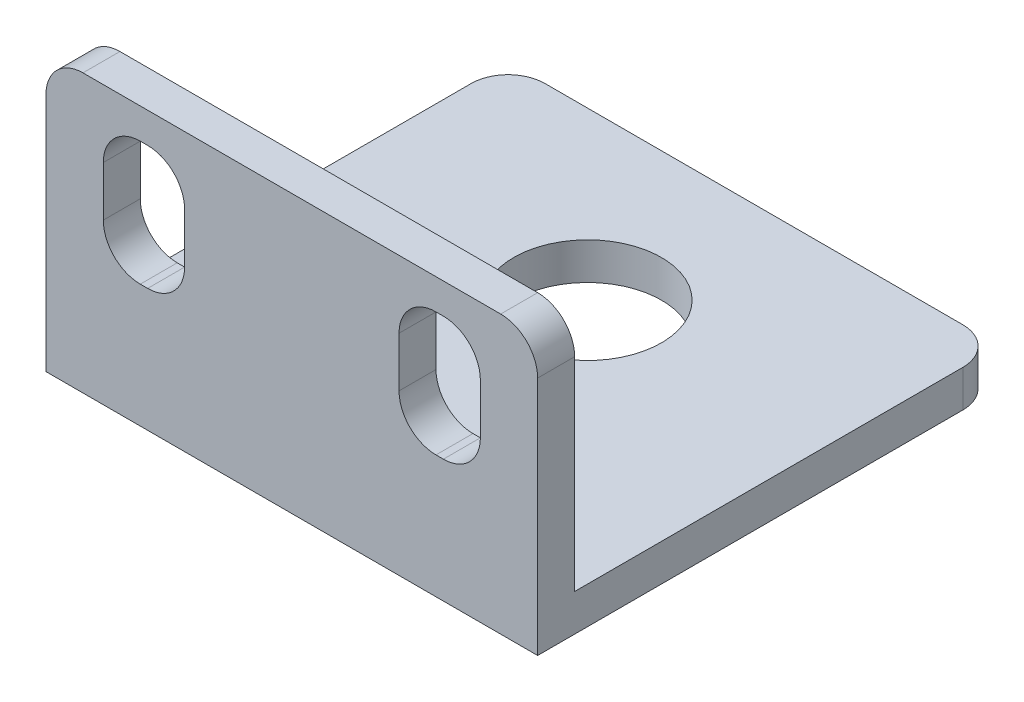
SolidWorks part; units mm, degrees
ref_plane "Front" through (0, 0, 0) normal (0, 0, 1) x (1, 0, 0)
ref_plane "Top" through (0, 0, 0) normal (0, 1, 0) x (1, 0, 0)
ref_plane "Right" through (0, 0, 0) normal (1, 0, 0) x (0, 0, -1)
sketch "Sketch1" plane through (0, 0, 0) normal (0, 1, 0) x (1, 0, 0)
  line L1 (13.3, -12.5) -> (-13.3, -12.5)
  line L2 (13.3, -12.5) -> (13.3, 12.5)
  line L3 (13.3, 12.5) -> (-13.3, 12.5)
  line L4 (-13.3, -12.5) -> (-13.3, 12.5)
  line L5 (13.3, -12.5) -> (-13.3, 12.5) construction
  line L6 (13.3, 12.5) -> (-13.3, -12.5) construction
  point P0 (0, 0)
  dimension "D1" = 26.6
  dimension "D2" = 25
extrude "Boss-Extrude1" add sketch "Sketch1" along normal blind 2
sketch "Sketch2" plane through (0, 2, 0) normal (0, 1, 0) x (1, 0, 0)
  line L0 (13.3, -12.5) -> (13.3, 12.5) construction
  line L1 (-13.3, -12.5) -> (13.3, -12.5)
  line L2 (-13.3, -12.5) -> (-13.3, -10.5)
  line L3 (-13.3, -10.5) -> (13.3, -10.5)
  line L4 (13.3, -12.5) -> (13.3, -10.5)
  dimension "D1" = 2
extrude "Boss-Extrude2" add sketch "Sketch2" along normal blind 13
sketch "Sketch3" plane through (0, 0, 10.5) normal (0, 0, -1) x (-1, 0, 0)
  line L1 (-10.2, 6.65) -> (-5.8, 6.65)
  line L2 (-10.2, 6.65) -> (-10.2, 13.35)
  line L3 (-10.2, 13.35) -> (-5.8, 13.35)
  line L4 (-5.8, 6.65) -> (-5.8, 13.35)
  line L5 (-10.2, 6.65) -> (-5.8, 13.35) construction
  line L6 (-10.2, 13.35) -> (-5.8, 6.65) construction
  line L7 (5.8, 6.65) -> (10.2, 6.65)
  line L8 (5.8, 6.65) -> (5.8, 13.35)
  line L9 (5.8, 13.35) -> (10.2, 13.35)
  line L10 (10.2, 6.65) -> (10.2, 13.35)
  line L11 (5.8, 6.65) -> (10.2, 13.35) construction
  line L12 (5.8, 13.35) -> (10.2, 6.65) construction
  line L14 (-13.3, 0) -> (13.3, 0) construction
  line L15 (0, 15) -> (0, 0) construction
  line L16 (-13.3, 15) -> (13.3, 15) construction
  point P0 (-8, 10)
  point P5 (8, 10)
  dimension "D1" = 4.4
  dimension "D2" = 4.4
  dimension "D3" = 6.7
  dimension "D4" = 6.7
  dimension "D5" = 8
  dimension "D6" = 10
  dimension "D7" = 8
  dimension "D8" = 10
extrude "Cut-Extrude1" cut sketch "Sketch3" against normal through all
fillet "Fillet1" radius 2 12 edges at (-13.3, 1, -12.5) (13.3, 1, -12.5) (5.8, 6.65, 11.5) (10.2, 6.65, 11.5) (-10.2, 6.65, 11.5) (-5.8, 6.65, 11.5) (-10.2, 13.35, 11.5) (-5.8, 13.35, 11.5) (5.8, 13.35, 11.5) (10.2, 13.35, 11.5) (13.3, 15, 11.5) (-13.3, 15, 11.5)
sketch "Sketch4" plane through (0, 2, 0) normal (0, 1, 0) x (1, 0, 0)
  line L0 (-11.3, -12.5) -> (11.3, -12.5) construction
  circle A0 centre (0, 3.5) radius 4
  dimension "D1" = 8
  dimension "D2" = 16
extrude "Cut-Extrude2" cut sketch "Sketch4" against normal through all
